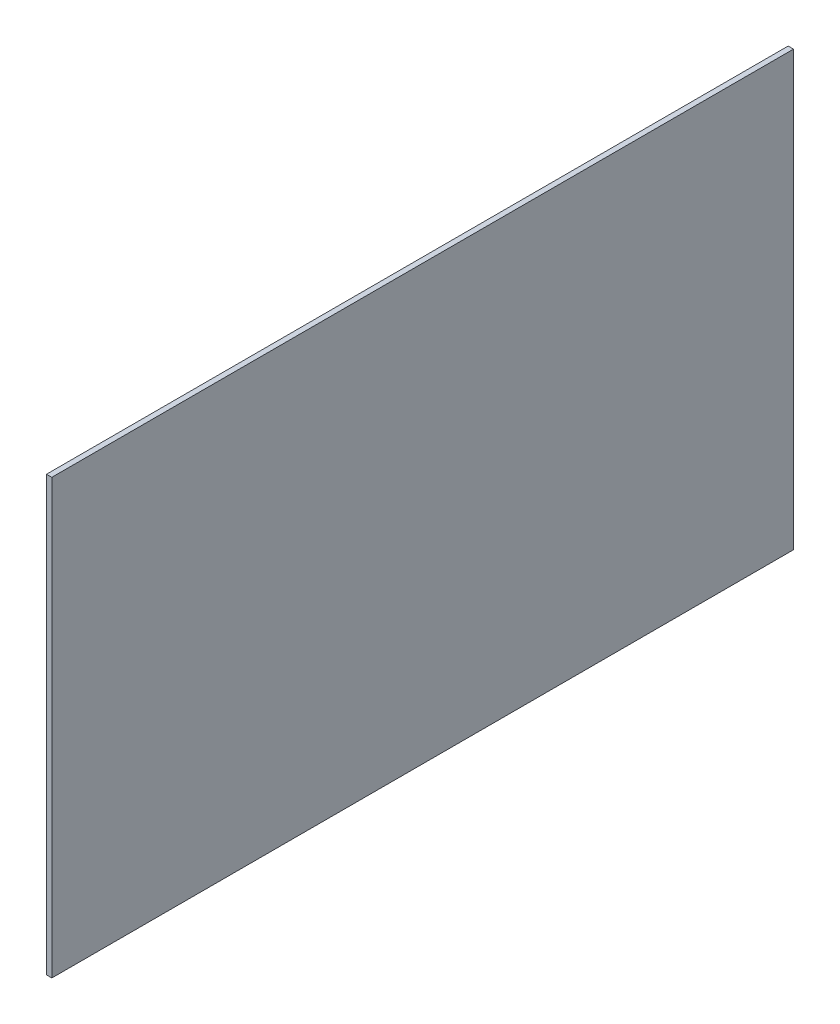
SolidWorks part; units mm, degrees
material "Glas"
ref_plane "Ebene vorne" through (0, 0, 0) normal (0, 0, 1) x (1, 0, 0)
ref_plane "Ebene oben" through (0, 0, 0) normal (0, 1, 0) x (1, 0, 0)
ref_plane "Ebene rechts" through (0, 0, 0) normal (1, 0, 0) x (0, 0, -1)
sketch "Skizze1" plane through (0, 0, 0) normal (1, 0, 0) x (0, 0, -1)
  line L1 (0, 1299) -> (-2222, 1299)
  line L2 (0, 1299) -> (0, 0)
  line L3 (0, 0) -> (-2222, 0)
  line L4 (-2222, 1299) -> (-2222, 0)
  dimension "Breite" = 2222
  dimension "Tiefe" = 1299
extrude "Aufsatz-Linear austragen1" add sketch "Skizze1" along normal blind 16
other "PropertyManager"
